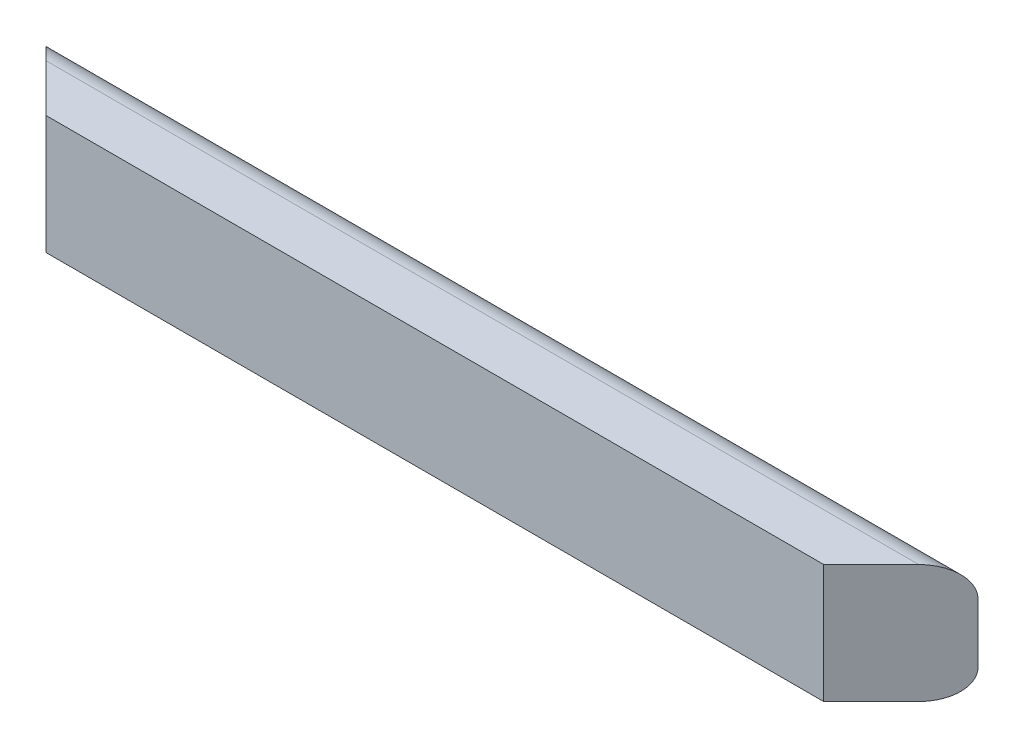
SolidWorks part; units mm, degrees
ref_plane "Front" through (0, 0, 0) normal (0, 0, 1) x (1, 0, 0)
ref_plane "Top" through (0, 0, 0) normal (0, 1, 0) x (1, 0, 0)
ref_plane "Right" through (0, 0, 0) normal (1, 0, 0) x (0, 0, -1)
sketch "Sketch1" plane through (0, 0, 0) normal (1, 0, 0) x (0, 0, -1)
  line L0 (0, 0) -> (0, 127) construction
  line L1 (0, 0) -> (31.75, 0)
  line L2 (31.75, 127) -> (0, 127)
  line L3 (63.5, 95.25) -> (63.5, 31.75)
  line L4 (0, 0) -> (-19.05, 0)
  line L5 (-19.05, 0) -> (-19.05, 127)
  line L6 (-19.05, 127) -> (0, 127)
  arc A0 (31.75, 0) -> (63.5, 31.75) centre (31.75, 31.75) ccw
  arc A1 (63.5, 95.25) -> (31.75, 127) centre (31.75, 95.25) ccw
  dimension "D2" = 63.5
  dimension "D1" = 19.05
extrude "Boss-Extrude1" add sketch "Sketch1" along normal blind 996.95
ref_plane "Mid_Plane" through (498.475, 0, 0) normal (1, 0, 0) x (0, 0, -1)
ref_plane "Plane1" through (466.725, 0, 466.725) normal (0.7071, 0, 0.7071) x (0, 1, 0)
sketch "Sketch2" plane through (466.725, 0, 466.725) normal (0.7071, 0, 0.7071) x (0, 1, 0)
  line L1 (205.1964, -433.0743) -> (-139.2061, -433.0743)
  line L2 (205.1964, -433.0743) -> (205.1964, -926.2875)
  line L3 (205.1964, -926.2875) -> (-139.2061, -926.2875)
  line L4 (-139.2061, -433.0743) -> (-139.2061, -926.2875)
  line L5 (205.1964, -433.0743) -> (-139.2061, -926.2875) construction
  line L6 (205.1964, -926.2875) -> (-139.2061, -433.0743) construction
  point P4 (32.9952, -679.6809)
extrude "Cut-Extrude1" cut sketch "Sketch2" along normal through all
mirror "Mirror1" about plane through (498.475, 0, 0) normal (1, 0, 0) of "Cut-Extrude1"
